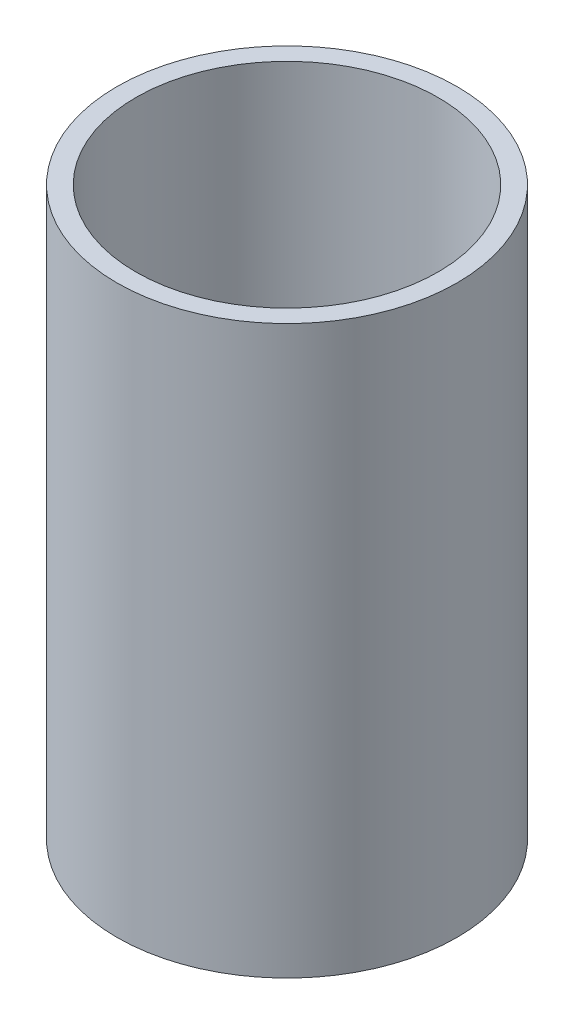
SolidWorks part; units mm, degrees
ref_plane "Front Plane" through (0, 0, 0) normal (0, 0, 1) x (1, 0, 0)
ref_plane "Top Plane" through (0, 0, 0) normal (0, 1, 0) x (1, 0, 0)
ref_plane "Right Plane" through (0, 0, 0) normal (1, 0, 0) x (0, 0, -1)
sketch "Sketch1" plane through (0, 0, 0) normal (0, 1, 0) x (1, 0, 0)
  circle A0 centre (0, 0) radius 28.575
  dimension "D1" = 57.15
extrude "Boss-Extrude1" add sketch "Sketch1" along normal blind 3.175
sketch "Sketch2" plane through (0, 3.175, 0) normal (0, 1, 0) x (1, 0, 0)
  circle A0 centre (0, 0) radius 28.575 construction
  circle A1 centre (0, 0) radius 28.575
  circle A4 centre (0, 0) radius 25.4
  circle A5 centre (0, 0) radius 25.4
  dimension "D1" = 3.175
extrude "Boss-Extrude2" add sketch "Sketch2" along normal blind 92.075
